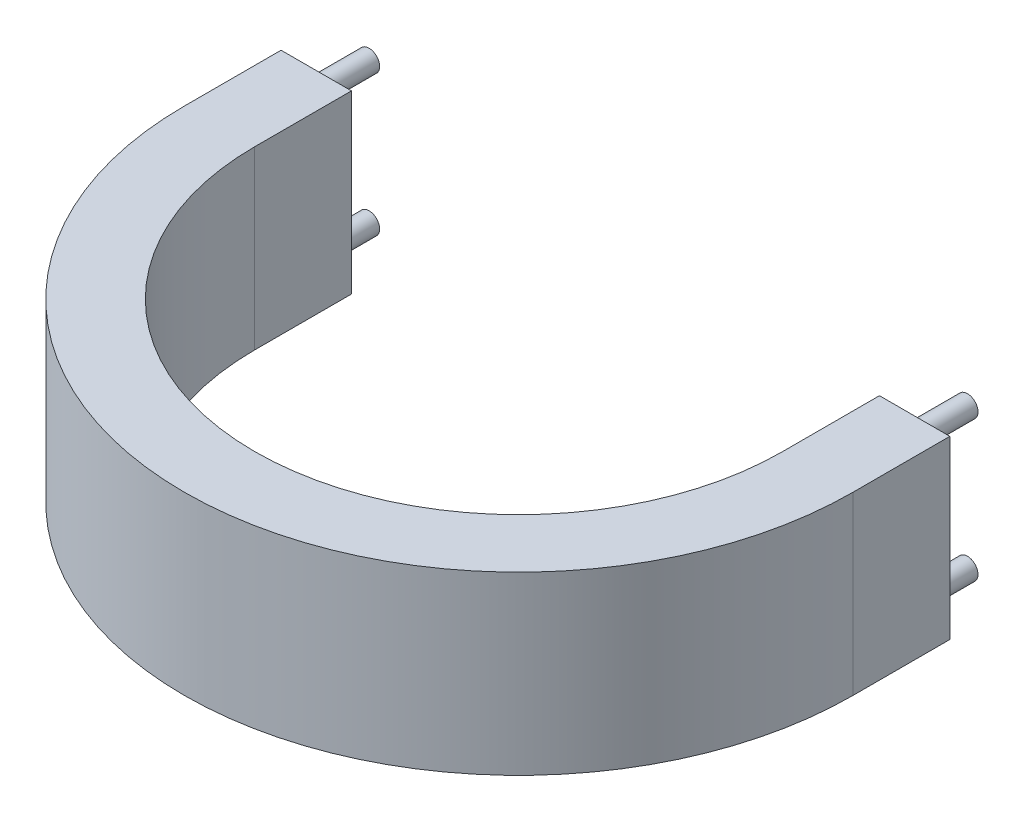
SolidWorks part; units mm, degrees
ref_plane "Front" through (0, 0, 0) normal (0, 0, 1) x (1, 0, 0)
ref_plane "Top" through (0, 0, 0) normal (0, 1, 0) x (1, 0, 0)
ref_plane "Right" through (0, 0, 0) normal (1, 0, 0) x (0, 0, -1)
sketch "草图2" plane through (0, 0, 0) normal (0, 1, 0) x (1, 0, 0)
  line L0 (-30, 0) -> (-30, 11)
  line L2 (-38, 0) -> (-38, 11)
  line L3 (-38, 11) -> (-30, 11)
  line L4 (38, 0) -> (38, 11)
  line L5 (30, 0) -> (30, 11)
  line L6 (30, 11) -> (38, 11)
  arc A0 (-38, 0) -> (38, 0) centre (0, 0) ccw
  arc A1 (-30, 0) -> (30, 0) centre (0, 0) ccw
  dimension "D1" = 11
extrude "凸台-拉伸1" add sketch "草图2" along normal blind 20
sketch "草图3" plane through (0, 0, -11) normal (0, 0, -1) x (-1, 0, 0)
  line L0 (-34, 20) -> (-34, 0) construction
  line L1 (-38, 20) -> (-30, 20) construction
  line L2 (-38, 0) -> (-30, 0) construction
  line L3 (34, 20) -> (34, 0) construction
  line L4 (30, 20) -> (38, 20) construction
  line L5 (30, 0) -> (38, 0) construction
  line L6 (-38, 10) -> (38, 10) construction
  line L7 (-38, 20) -> (-38, 0) construction
  line L8 (38, 20) -> (38, 0) construction
  circle A0 centre (-34, 18) radius 1.2
  circle A1 centre (-34, 2) radius 1.2
  circle A2 centre (34, 18) radius 1.2
  circle A3 centre (34, 2) radius 1.2
  point P26 (0, 0)
extrude "凸台-拉伸2" add sketch "草图3" along normal blind 6
